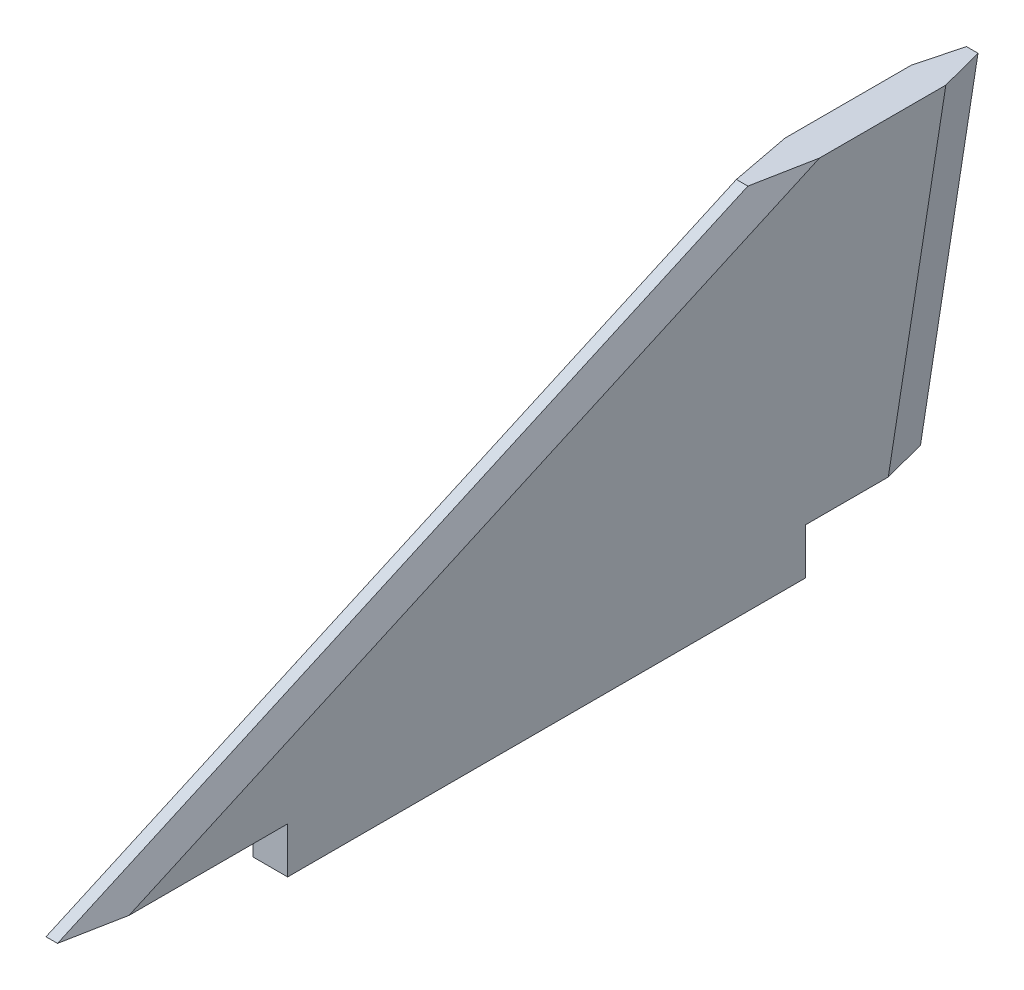
SolidWorks part; units mm, degrees
material "Pine"
ref_plane "Front Plane" through (0, 0, 0) normal (0, 0, 1) x (1, 0, 0)
ref_plane "Top Plane" through (0, 0, 0) normal (0, 1, 0) x (1, 0, 0)
ref_plane "Right Plane" through (0, 0, 0) normal (1, 0, 0) x (0, 0, -1)
sketch "Sketch1" plane through (0, 0, 0) normal (1, 0, 0) x (0, 0, -1)
  line L0 (0, 0) -> (0, 4)
  line L1 (0, 4) -> (-19, 4)
  line L2 (-19, 4) -> (41, 31)
  line L3 (41, 31) -> (61, 31)
  line L4 (61, 31) -> (56, 4)
  line L5 (56, 4) -> (45, 4)
  line L6 (45, 4) -> (45, 0)
  line L7 (45, 0) -> (0, 0)
  line L8 (-19, 4) -> (56, 4) construction
  line L9 (56, 4) -> (56, 2.5) construction
  line L10 (45, 4) -> (48.5, 4)
  arc A0 (56, 2.5) -> (48.5, 4) centre (48.5, -15.5) ccw construction
  dimension "D1" = 45
  dimension "D2" = 75
  dimension "D3" = 4
  dimension "D4" = 20
  dimension "D5" = 60
  dimension "D6" = 27
  dimension "D7" = 11
  dimension "D8" = 3.5
  dimension "D9" = 1.5
extrude "Boss-Extrude1" add sketch "Sketch1" along normal mid plane 3 contours L7 L6 L5 L4 L3 L2 L1 L0
chamfer "Chamfer1" distance 1 angle 75 2 edges at (1.5, 17.5, -58.5) (-1.5, 17.5, -58.5)
chamfer "Chamfer2" distance 1 angle 65 2 edges at (-1.5, 17.5, -11) (1.5, 17.5, -11)
